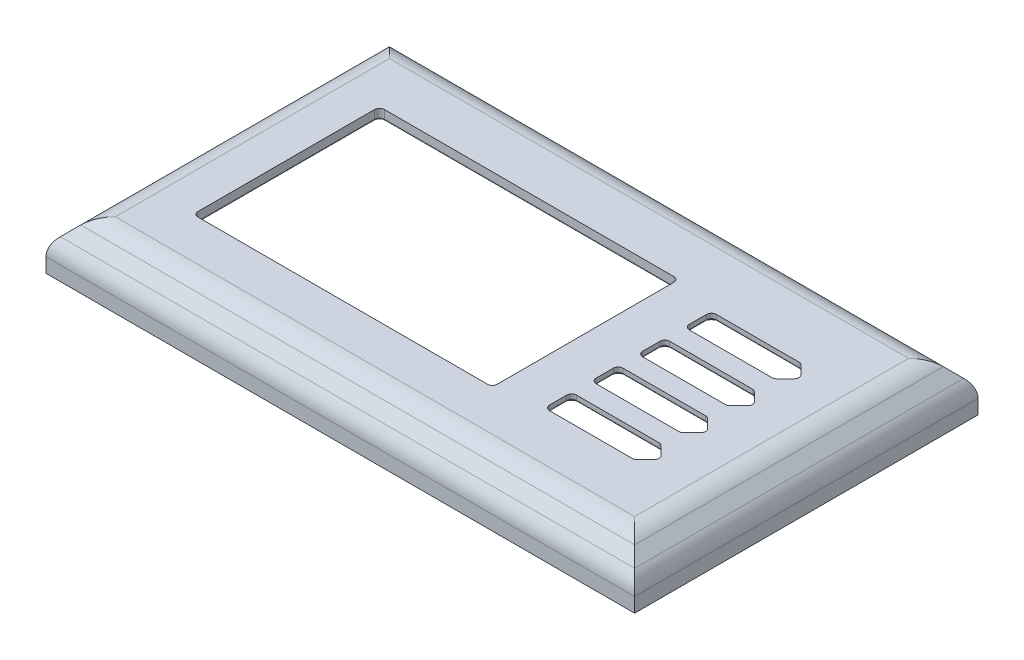
SolidWorks part; units mm, degrees
material "ABS"
ref_plane "Front Plane" through (0, 0, 0) normal (0, 0, 1) x (1, 0, 0)
ref_plane "Top Plane" through (0, 0, 0) normal (0, 1, 0) x (1, 0, 0)
ref_plane "Right Plane" through (0, 0, 0) normal (1, 0, 0) x (0, 0, -1)
sketch "Sketch1" plane through (0, 0, 0) normal (0, 1, 0) x (1, 0, 0)
  line L1 (0, 0) -> (120, 0)
  line L2 (0, 0) -> (0, 70)
  line L3 (0, 70) -> (120, 70)
  line L4 (120, 0) -> (120, 70)
  dimension "D1" = 120
  dimension "D2" = 70
extrude "Boss-Extrude1" add sketch "Sketch1" along normal blind 10
chamfer "Chamfer1" distance 5 angle 45 4 edges at (120, 10, -35) (60, 10, -70) (0, 10, -35) (60, 10, 0)
shell "Shell1" thickness 2
sketch "Sketch2" plane through (0, 10, 0) normal (0, 1, 0) x (1, 0, 0)
  line L0 (45.0677, 53.4274) -> (45.0677, 65) construction
  line L1 (14.5677, 53.4274) -> (75.5677, 53.4274)
  line L2 (14.5677, 53.4274) -> (14.5677, 15.4274)
  line L3 (14.5677, 15.4274) -> (75.5677, 15.4274)
  line L4 (75.5677, 53.4274) -> (75.5677, 15.4274)
  line L5 (84.5677, 36.0831) -> (102.8177, 36.0831)
  line L6 (102.8177, 51.0831) -> (105.5677, 48.3331)
  line L7 (115, 65) -> (5, 65) construction
  line L8 (45.0677, 15.4274) -> (45.0677, 5) construction
  line L9 (5, 5) -> (115, 5) construction
  line L10 (84.5677, 51.0831) -> (102.8177, 51.0831)
  line L11 (84.5677, 51.0831) -> (84.5677, 45.5831)
  line L12 (84.5677, 45.5831) -> (102.8177, 45.5831)
  line L13 (84.5677, 48.3331) -> (105.5677, 48.3331) construction
  line L14 (105.5677, 48.3331) -> (102.8177, 45.5831)
  line L15 (84.5677, 41.5831) -> (84.5677, 36.0831)
  line L16 (84.5677, 41.5831) -> (102.8177, 41.5831)
  line L17 (102.8177, 41.5831) -> (105.5677, 38.8331)
  line L18 (105.5677, 38.8331) -> (102.8177, 36.0831)
  line L19 (84.5677, 26.5831) -> (102.8177, 26.5831)
  line L20 (84.5677, 32.0831) -> (84.5677, 26.5831)
  line L21 (84.5677, 32.0831) -> (102.8177, 32.0831)
  line L22 (102.8177, 32.0831) -> (105.5677, 29.3331)
  line L23 (105.5677, 29.3331) -> (102.8177, 26.5831)
  line L24 (84.5677, 17.0831) -> (102.8177, 17.0831)
  line L25 (84.5677, 22.5831) -> (84.5677, 17.0831)
  line L26 (84.5677, 22.5831) -> (102.8177, 22.5831)
  line L27 (102.8177, 22.5831) -> (105.5677, 19.8331)
  line L28 (105.5677, 19.8331) -> (102.8177, 17.0831)
  dimension "D3" = 5.5
  dimension "D1" = 61
  dimension "D2" = 38
  dimension "D4" = 135
  dimension "D5" = 21
  dimension "D7" = 9
  dimension "D8" = 4
  dimension "D6" = 4
extrude "Cut-Extrude1" cut sketch "Sketch2" against normal through all
fillet "Fillet8" radius 1 24 edges at (75.5677, 9, -15.4274) (75.5677, 9, -53.4274) (14.5677, 9, -53.4274) (14.5677, 9, -15.4274) (102.8177, 9, -45.5831) (102.8177, 9, -51.0831) (84.5677, 9, -45.5831) (102.8177, 9, -36.0831) (102.8177, 9, -41.5831) (102.8177, 9, -26.5831) (102.8177, 9, -32.0831) (102.8177, 9, -17.0831) (102.8177, 9, -22.5831) (84.5677, 9, -36.0831) (84.5677, 9, -26.5831) (84.5677, 9, -17.0831) (84.5677, 9, -22.5831) (84.5677, 9, -32.0831) (84.5677, 9, -41.5831) (84.5677, 9, -51.0831) (105.5677, 9, -19.8331) (105.5677, 9, -29.3331) (105.5677, 9, -38.8331) (105.5677, 9, -48.3331)
fillet "Fillet10" radius 5 16 edges at (118, 4.1716, -35) (114.1716, 8, -35) (60, 4.1716, -68) (60, 8, -64.1716) (2, 4.1716, -35) (5.8284, 8, -35) (60, 4.1716, -2) (60, 8, -5.8284) (120, 5, -35) (60, 5, -70) (0, 5, -35) (60, 10, -65) (5, 10, -35) (60, 5, 0) (60, 10, -5) (115, 10, -35)
sketch "Sketch3" plane through (0, 8, 0) normal (0, -1, 0) x (1, 0, 0)
  line L36 (83.5677, -31.0831) -> (83.5677, -27.5831)
  line L37 (102.4034, -33.0831) -> (85.5677, -33.0831)
  line L38 (105.5677, -30.7473) -> (103.8177, -32.4973)
  line L39 (103.8177, -26.1689) -> (105.5677, -27.9189)
  line L40 (103.8177, -16.6689) -> (105.5677, -18.4189)
  line L41 (105.5677, -21.2473) -> (103.8177, -22.9973)
  line L42 (102.4034, -23.5831) -> (85.5677, -23.5831)
  line L43 (83.5677, -21.5831) -> (83.5677, -18.0831)
  line L44 (85.5677, -16.0831) -> (102.4034, -16.0831)
  line L45 (103.8177, -16.6689) -> (105.5677, -18.4189)
  line L46 (105.5677, -21.2473) -> (103.8177, -22.9973)
  line L47 (102.4034, -23.5831) -> (85.5677, -23.5831)
  line L48 (83.5677, -21.5831) -> (83.5677, -18.0831)
  line L49 (85.5677, -16.0831) -> (102.4034, -16.0831)
  line L50 (85.5677, -25.5831) -> (102.4034, -25.5831)
  line L51 (83.5677, -40.5831) -> (83.5677, -37.0831)
  line L52 (102.4034, -42.5831) -> (85.5677, -42.5831)
  line L53 (105.5677, -40.2473) -> (103.8177, -41.9973)
  line L54 (103.8177, -35.6689) -> (105.5677, -37.4189)
  line L55 (85.5677, -35.0831) -> (102.4034, -35.0831)
  line L56 (83.5677, -50.0831) -> (83.5677, -46.5831)
  line L57 (102.4034, -52.0831) -> (85.5677, -52.0831)
  line L58 (105.5677, -49.7473) -> (103.8177, -51.4973)
  line L59 (103.8177, -45.1689) -> (105.5677, -46.9189)
  line L60 (85.5677, -44.5831) -> (102.4034, -44.5831)
  arc A20 (83.5677, -31.0831) -> (85.5677, -33.0831) centre (85.5677, -31.0831) ccw
  arc A21 (103.8177, -16.6689) -> (102.4034, -16.0831) centre (102.4034, -18.0831) ccw
  arc A22 (103.8177, -16.6689) -> (102.4034, -16.0831) centre (102.4034, -18.0831) ccw
  arc A23 (102.4034, -23.5831) -> (103.8177, -22.9973) centre (102.4034, -21.5831) ccw
  arc A24 (105.5677, -21.2473) -> (105.5677, -18.4189) centre (104.1534, -19.8331) ccw
  arc A25 (83.5677, -21.5831) -> (85.5677, -23.5831) centre (85.5677, -21.5831) ccw
  arc A26 (85.5677, -16.0831) -> (83.5677, -18.0831) centre (85.5677, -18.0831) ccw
  arc A27 (102.4034, -23.5831) -> (103.8177, -22.9973) centre (102.4034, -21.5831) ccw
  arc A28 (105.5677, -21.2473) -> (105.5677, -18.4189) centre (104.1534, -19.8331) ccw
  arc A29 (83.5677, -21.5831) -> (85.5677, -23.5831) centre (85.5677, -21.5831) ccw
  arc A30 (85.5677, -16.0831) -> (83.5677, -18.0831) centre (85.5677, -18.0831) ccw
  arc A31 (102.4034, -33.0831) -> (103.8177, -32.4973) centre (102.4034, -31.0831) ccw
  arc A32 (105.5677, -30.7473) -> (105.5677, -27.9189) centre (104.1534, -29.3331) ccw
  arc A33 (103.8177, -26.1689) -> (102.4034, -25.5831) centre (102.4034, -27.5831) ccw
  arc A34 (85.5677, -25.5831) -> (83.5677, -27.5831) centre (85.5677, -27.5831) ccw
  arc A35 (83.5677, -40.5831) -> (85.5677, -42.5831) centre (85.5677, -40.5831) ccw
  arc A36 (102.4034, -42.5831) -> (103.8177, -41.9973) centre (102.4034, -40.5831) ccw
  arc A37 (105.5677, -40.2473) -> (105.5677, -37.4189) centre (104.1534, -38.8331) ccw
  arc A38 (103.8177, -35.6689) -> (102.4034, -35.0831) centre (102.4034, -37.0831) ccw
  arc A39 (85.5677, -35.0831) -> (83.5677, -37.0831) centre (85.5677, -37.0831) ccw
  arc A40 (83.5677, -50.0831) -> (85.5677, -52.0831) centre (85.5677, -50.0831) ccw
  arc A41 (102.4034, -52.0831) -> (103.8177, -51.4973) centre (102.4034, -50.0831) ccw
  arc A42 (105.5677, -49.7473) -> (105.5677, -46.9189) centre (104.1534, -48.3331) ccw
  arc A43 (103.8177, -45.1689) -> (102.4034, -44.5831) centre (102.4034, -46.5831) ccw
  arc A44 (85.5677, -44.5831) -> (83.5677, -46.5831) centre (85.5677, -46.5831) ccw
  dimension "D4" = 2
  dimension "D1" = 1
  dimension "D2" = 1
  dimension "D3" = 4
extrude "Cut-Extrude3" cut sketch "Sketch3" against normal blind 0.8
fillet "Fillet12" radius 0.3 80 edges at (84.8605, 8.8, -22.2902) (93.9855, 8.8, -22.5831) (102.7861, 8.8, -22.5069) (103.9855, 8.8, -21.4152) (105.1534, 8.8, -19.8331) (103.9855, 8.8, -18.251) (102.7861, 8.8, -17.1592) (93.9855, 8.8, -17.0831) (84.8605, 8.8, -17.376) (84.8605, 8.8, -31.7902) (93.9855, 8.8, -32.0831) (102.7861, 8.8, -32.0069) (103.9855, 8.8, -30.9152) (105.1534, 8.8, -29.3331) (103.9855, 8.8, -27.751) (102.7861, 8.8, -26.6592) (93.9855, 8.8, -26.5831) (84.8605, 8.8, -26.876) (84.8605, 8.8, -41.2902) (93.9855, 8.8, -41.5831) (102.7861, 8.8, -41.5069) (103.9855, 8.8, -40.4152) (105.1534, 8.8, -38.8331) (103.9855, 8.8, -37.251) (102.7861, 8.8, -36.1592) (93.9855, 8.8, -36.0831) (84.8605, 8.8, -36.376) (84.8605, 8.8, -50.7902) (93.9855, 8.8, -51.0831) (102.7861, 8.8, -51.0069) (103.9855, 8.8, -49.9152) (105.1534, 8.8, -48.3331) (103.9855, 8.8, -46.751) (102.7861, 8.8, -45.6592) (93.9855, 8.8, -45.5831) (84.8605, 8.8, -45.876) (84.1534, 8, -45.1689) (93.9855, 8, -44.5831) (103.1688, 8, -44.7353) (104.6927, 8, -46.0439) (106.1534, 8, -48.3331) (104.6927, 8, -50.6223) (103.1688, 8, -51.9308) (93.9855, 8, -52.0831) (84.1534, 8, -51.4973) (84.1534, 8, -35.6689) (93.9855, 8, -35.0831) (103.1688, 8, -35.2353) (104.6927, 8, -36.5439) (106.1534, 8, -38.8331) (104.6927, 8, -41.1223) (103.1688, 8, -42.4308) (93.9855, 8, -42.5831) (84.1534, 8, -41.9973) (84.1534, 8, -26.1689) (93.9855, 8, -25.5831) (103.1688, 8, -25.7353) (104.6927, 8, -27.0439) (106.1534, 8, -29.3331) (104.6927, 8, -31.6223) (103.1688, 8, -32.9308) (93.9855, 8, -33.0831) (84.1534, 8, -32.4973) (84.1534, 8, -16.6689) (93.9855, 8, -16.0831) (103.1688, 8, -16.2353) (104.6927, 8, -17.5439) (106.1534, 8, -19.8331) (104.6927, 8, -22.1223) (103.1688, 8, -23.4308) (93.9855, 8, -23.5831) (84.1534, 8, -22.9973) (84.5677, 8.8, -19.8331) (84.5677, 8.8, -29.3331) (84.5677, 8.8, -38.8331) (84.5677, 8.8, -48.3331) (83.5677, 8, -48.3331) (83.5677, 8, -38.8331) (83.5677, 8, -29.3331) (83.5677, 8, -19.8331)
fillet "Fillet13" radius 0.3 8 edges at (75.2748, 8, -53.1345) (75.5677, 8, -34.4274) (75.2748, 8, -15.7203) (45.0677, 8, -15.4274) (14.8605, 8, -15.7203) (14.5677, 8, -34.4274) (14.8605, 8, -53.1345) (45.0677, 8, -53.4274)
sketch "Sketch4" plane through (0, 0, 0) normal (0, -1, 0) x (1, 0, 0)
  line L0 (2, -2) -> (118, -2) construction
  line L1 (1.9, -1.9) -> (118.1, -1.9)
  line L2 (1.9, -1.9) -> (1.9, -68.1)
  line L3 (1.9, -68.1) -> (118.1, -68.1)
  line L4 (118.1, -1.9) -> (118.1, -68.1)
  line L5 (2, -68) -> (2, -2) construction
  line L6 (118, -68) -> (2, -68) construction
  line L7 (118, -2) -> (118, -68) construction
  dimension "D1" = 0.1
  dimension "D2" = 0.1
  dimension "D3" = 0.1
  dimension "D4" = 0.1
extrude "Cut-Extrude6" cut sketch "Sketch4" against normal blind 2 contours L2 L3 L4 L1
